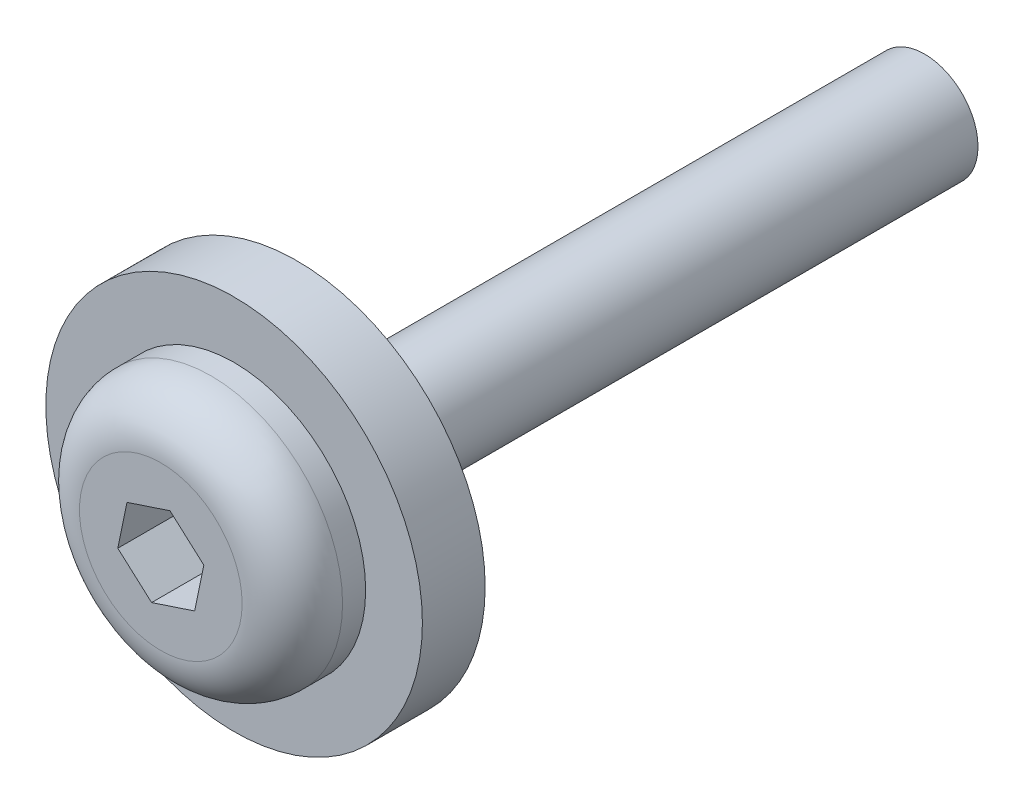
SolidWorks part; units mm, degrees
material "AISI 304"
ref_plane "Front Plane" through (0, 0, 0) normal (0, 0, 1) x (1, 0, 0)
ref_plane "Top Plane" through (0, 0, 0) normal (0, 1, 0) x (1, 0, 0)
ref_plane "Right Plane" through (0, 0, 0) normal (1, 0, 0) x (0, 0, -1)
sketch "Sketch1" plane through (0, 0, 0) normal (0, 0, 1) x (1, 0, 0)
  circle A0 centre (0, 0) radius 1.3526
  dimension "D1" = 2.7051
extrude "Boss-Extrude1" add sketch "Sketch1" along normal blind 15.875
sketch "Sketch2" plane through (0, 0, 15.875) normal (0, 0, 1) x (1, 0, 0)
  circle A0 centre (0, 0) radius 4.7625
  dimension "D1" = 9.525
extrude "Boss-Extrude2" add sketch "Sketch2" along normal blind 1.5875
sketch "Sketch3" plane through (0, 0, 17.4625) normal (0, 0, 1) x (1, 0, 0)
  circle A0 centre (0, 0) radius 3.3274
  dimension "D1" = 6.6548
extrude "Boss-Extrude3" add sketch "Sketch3" along normal blind 1.8542
fillet "Fillet1" radius 1.27 1 edges at (3.3274, 0, 19.3167)
sketch "Sketch4" plane through (0, 0, 19.3167) normal (0, 0, 1) x (1, 0, 0)
  line L1 (1.0878, 0.3595) -> (0.2325, 1.1218)
  line L2 (0.2325, 1.1218) -> (-0.8553, 0.7623)
  line L3 (-0.8553, 0.7623) -> (-1.0878, -0.3595)
  line L4 (-1.0878, -0.3595) -> (-0.2325, -1.1218)
  line L5 (-0.2325, -1.1218) -> (0.8553, -0.7623)
  line L6 (0.8553, -0.7623) -> (1.0878, 0.3595)
  circle A0 centre (0, 0) radius 0.9922 construction
  dimension "D1" = 1.9844
extrude "Cut-Extrude1" cut sketch "Sketch4" against normal blind 1.8542
